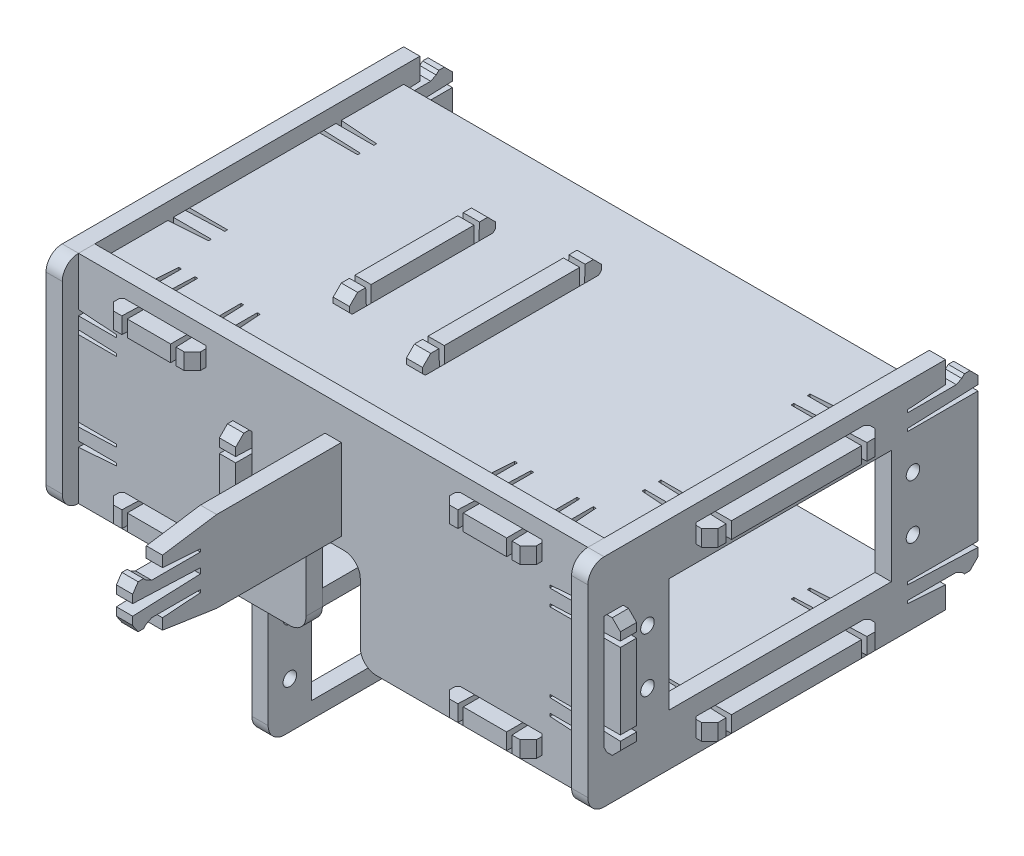
SolidWorks part; units mm, degrees
material "Lasercut ABS"
ref_plane "Front Plane" through (0, 0, 0) normal (0, 0, 1) x (1, 0, 0)
ref_plane "Top Plane" through (0, 0, 0) normal (0, 1, 0) x (1, 0, 0)
ref_plane "Right Plane" through (0, 0, 0) normal (1, 0, 0) x (0, 0, -1)
ref_plane "Plane1" through (47, 0, 0) normal (1, 0, 0) x (0, 0, -1)
ref_plane "Plane2" through (-47, 0, 0) normal (1, 0, 0) x (0, 0, -1)
sketch "Sketch1" plane through (47, 0, 0) normal (1, 0, 0) x (0, 0, -1)
  line L0 (36.5, 12) -> (36.5, -12)
  line L1 (-32.5, 10) -> (-29.5, 10)
  line L2 (-32.5, 10) -> (-32.5, -10)
  line L3 (-32.5, -10) -> (-29.5, -10)
  line L4 (-29.5, 10) -> (-29.5, -10)
  line L5 (-15, 17) -> (15, 17)
  line L6 (-15, 17) -> (-15, 14)
  line L7 (-15, 14) -> (15, 14)
  line L8 (15, 17) -> (15, 14)
  line L9 (-15, -14) -> (15, -14)
  line L10 (-15, -14) -> (-15, -17)
  line L11 (-15, -17) -> (15, -17)
  line L12 (15, -14) -> (15, -17)
  line L13 (30.5, 16) -> (30.5, 20)
  line L14 (30.5, 20) -> (-35.5, 20)
  line L15 (-35.5, 20) -> (-35.5, -20)
  line L16 (-35.5, -20) -> (30.5, -20)
  line L17 (30.5, -20) -> (30.5, -16)
  point P21 (0, -14)
  point P22 (-32.5, 0)
  point P23 (36.5, 0)
  line B0 (-24.5, 5) -> (-24.5, -5) construction
  line B1 (-20.5, -10.5) -> (20.5, -10.5)
  line B2 (-20.5, -10.5) -> (-20.5, 10.5)
  line B3 (-20.5, 10.5) -> (20.5, 10.5)
  line B4 (20.5, -10.5) -> (20.5, 10.5)
  line B5 (-20.5, -10.5) -> (20.5, 10.5) construction
  line B6 (-20.5, 10.5) -> (20.5, -10.5) construction
  line B7 (24.5, 5) -> (24.5, -5) construction
  line B8 (-24.5, 0) -> (24.5, 0) construction
  circle B9 centre (-24.5, 5) radius 1.25
  circle B10 centre (-24.5, -5) radius 1.25
  circle B11 centre (24.5, -5) radius 1.25
  circle B12 centre (24.5, 5) radius 1.25
  line B13 (23.5, -15.5) -> (30.5, -16)
  line B14 (23.5, -15) -> (23.5, -15.5)
  line B15 (32.5, -15) -> (23.5, -15)
  line B16 (33.5, -15.5) -> (32.5, -15)
  line B17 (34, -16) -> (33.5, -15.5)
  line B18 (35, -16) -> (34, -16)
  line B19 (36.5, -14.5) -> (35, -16)
  line B20 (36.5, -13) -> (36.5, -14.5)
  line B21 (23.5, -12) -> (23.5, -12.5)
  line B22 (23.5, -12.5) -> (36.5, -13)
  line B23 (36.5, -12) -> (23.5, -12)
  line B24 (36.5, 12) -> (23.5, 12)
  line B25 (23.5, 12) -> (23.5, 12.5)
  line B26 (23.5, 12.5) -> (36.5, 13)
  line B27 (36.5, 13) -> (36.5, 14.5)
  line B28 (36.5, 14.5) -> (35, 16)
  line B29 (35, 16) -> (34, 16)
  line B30 (34, 16) -> (33.5, 15.5)
  line B31 (33.5, 15.5) -> (32.5, 15)
  line B32 (32.5, 15) -> (23.5, 15)
  line B33 (23.5, 15) -> (23.5, 15.5)
  line B34 (23.5, 15.5) -> (30.5, 16)
  dimension "D1" = 3
  dimension "D2" = 14
  dimension "D3" = 14
  dimension "D4" = 3
  dimension "D5" = 3
  dimension "D6" = 30
  dimension "D7" = 30
  dimension "D8" = 9
  dimension "D9" = 3
  dimension "D10" = 20
  dimension "D11" = 3
sketch_block_instance "Block-Servo-Std-1"
sketch_block "Block-Servo-Std" parameters "D3"=2.5, "D1"=41, "D2"=21, "D4"=10, "D5"=49
sketch_block_instance "Block-Snap-L-1"
sketch_block "Block-Snap-L" parameters "D1"=13, "D2"=0.5, "D3"=1, "D4"=1.5, "D5"=1.5, "D6"=0.5, "D7"=1, "D8"=7, "D9"=1, "D10"=0.5, "D11"=1, "D12"=1.5, "D13"=2.5
sketch_block_instance "Block-Snap-R-1"
sketch_block "Block-Snap-R" parameters "D1"=13, "D2"=0.5, "D3"=1, "D4"=0.5, "D5"=1, "D6"=2.5, "D7"=1.5, "D8"=1.5, "D9"=1.5, "D10"=1, "D11"=0.5, "D12"=1, "D13"=7
extrude "Boss-Extrude1" add sketch "Sketch1" along normal blind 3 contours B33 B34 L13 L14 L15 L16 L17 B13 B14 B15 B16 B17 B18 B19 B20 B22 B21 B23 L0 B24 B25 B26 B27 B28 B29 B30 B31 B32 L9 L12 L11 L10 L1 L4 L3 L2 L5 L8 L7 L6 B4 B1 B2 B3 B9
mirror "Mirror2" about plane through (0, 0, 0) normal (1, 0, 0) of bodies 101
sketch "Sketch2" plane through (0, 0, 0) normal (1, 0, 0) x (0, 0, -1)
  line L0 (-13.5, 20) -> (11.5, 20)
  line L1 (15.5, 14) -> (27.5, 14)
  line L2 (27.5, 14) -> (27.5, -14)
  line L3 (27.5, -14) -> (24.5, -14)
  line L4 (-17.5, 14) -> (-55.5, 14)
  line L5 (-35.5, 20) -> (-35.5, -20) construction
  line L6 (-55.5, -1) -> (5.5, -1)
  line L7 (5.5, -1) -> (5.5, -14)
  line L8 (5.5, -14) -> (8.5, -14)
  line L9 (-15, 14) -> (15, 14) construction
  line L10 (30.5, 16) -> (30.5, 20) construction
  line L11 (-15, -14) -> (15, -14) construction
  line L12 (-29.5, 10) -> (-29.5, -10) construction
  line B0 (12.5, -20) -> (20.5, -20)
  line B1 (20.5, -20) -> (20.5, -7)
  line B2 (20.5, -7) -> (21, -7)
  line B3 (21, -7) -> (21.5, -20)
  line B4 (21.5, -20) -> (23, -20)
  line B5 (23, -20) -> (24.5, -18.5)
  line B6 (24.5, -18.5) -> (24.5, -17.5)
  line B7 (24.5, -17.5) -> (24, -17)
  line B8 (24, -17) -> (23.5, -16)
  line B9 (23.5, -16) -> (23.5, -7)
  line B10 (23.5, -7) -> (24, -7)
  line B11 (24, -7) -> (24.5, -14)
  line B12 (16.5, -20) -> (16.5, -7) construction
  line B13 (9, -7) -> (8.5, -14)
  line B14 (9.5, -7) -> (9, -7)
  line B15 (9.5, -16) -> (9.5, -7)
  line B16 (9, -17) -> (9.5, -16)
  line B17 (8.5, -17.5) -> (9, -17)
  line B18 (8.5, -18.5) -> (8.5, -17.5)
  line B19 (10, -20) -> (8.5, -18.5)
  line B20 (11.5, -20) -> (10, -20)
  line B21 (12.5, -7) -> (12, -7)
  line B22 (12, -7) -> (11.5, -20)
  line B23 (12.5, -20) -> (12.5, -7)
  line B24 (15, 7) -> (15.5, 14)
  line B25 (14.5, 7) -> (15, 7)
  line B26 (14.5, 16) -> (14.5, 7)
  line B27 (15, 17) -> (14.5, 16)
  line B28 (15.5, 17.5) -> (15, 17)
  line B29 (15.5, 18.5) -> (15.5, 17.5)
  line B30 (14, 20) -> (15.5, 18.5)
  line B31 (12.5, 20) -> (14, 20)
  line B32 (11.5, 7) -> (12, 7)
  line B33 (12, 7) -> (12.5, 20)
  line B34 (11.5, 20) -> (11.5, 7)
  line B35 (-13.5, 20) -> (-13.5, 7)
  line B36 (-13.5, 7) -> (-14, 7)
  line B37 (-14, 7) -> (-14.5, 20)
  line B38 (-14.5, 20) -> (-16, 20)
  line B39 (-16, 20) -> (-17.5, 18.5)
  line B40 (-17.5, 18.5) -> (-17.5, 17.5)
  line B41 (-17.5, 17.5) -> (-17, 17)
  line B42 (-17, 17) -> (-16.5, 16)
  line B43 (-16.5, 16) -> (-16.5, 7)
  line B44 (-16.5, 7) -> (-17, 7)
  line B45 (-17, 7) -> (-17.5, 14)
  line B46 (-55.5, 6.5) -> (-58.5, 6.5) construction
  line B47 (-58.5, 6) -> (-58.5, 7)
  line B48 (-58.5, 6) -> (-71, 5.5)
  line B49 (-71, 5.5) -> (-71, 4)
  line B50 (-71, 4) -> (-70, 2.5)
  line B51 (-70, 2.5) -> (-69, 2.5)
  line B52 (-69, 2.5) -> (-68.5, 3)
  line B53 (-68.5, 3) -> (-67.5, 3.5)
  line B54 (-67.5, 3.5) -> (-58.5, 3.5)
  line B55 (-58.5, 3.5) -> (-58.5, 3)
  line B56 (-58.5, 3) -> (-65.5, 2.5)
  line B57 (-65.5, 2.5) -> (-65.5, 0.5)
  line B58 (-65.5, 0.5) -> (-55.5, -1)
  line B59 (-58.5, 7) -> (-71, 7.5)
  line B60 (-71, 7.5) -> (-71, 9)
  line B61 (-71, 9) -> (-70, 10.5)
  line B62 (-70, 10.5) -> (-69, 10.5)
  line B63 (-69, 10.5) -> (-68.5, 10)
  line B64 (-68.5, 10) -> (-67.5, 9.5)
  line B65 (-67.5, 9.5) -> (-58.5, 9.5)
  line B66 (-58.5, 9.5) -> (-58.5, 10)
  line B67 (-58.5, 10) -> (-65.5, 10.5)
  line B68 (-65.5, 10.5) -> (-65.5, 12.5)
  line B69 (-65.5, 12.5) -> (-55.5, 14)
  dimension "D1" = 3
  dimension "D2" = 22
  dimension "D3" = 30
  dimension "D4" = 12
  dimension "D6" = 12
sketch_block_instance "Block-Snap-14mm-1"
sketch_block "Block-Snap-14mm" parameters "D1"=8, "D2"=13, "D3"=0.5, "D4"=1, "D5"=0.5, "D6"=1, "D7"=2.5, "D8"=1.5, "D9"=1.5, "D10"=1.5, "D11"=1, "D12"=0.5, "D13"=1, "D14"=7
sketch_block_instance "Block-Snap-L-3"
sketch_block_instance "Block-Snap-R-3"
sketch_block_instance "Block-Snap-Textile-1"
sketch_block "Block-Snap-Textile" parameters "D1"=3, "D2"=1, "D3"=2, "D4"=1.5, "D5"=10, "D6"=0.5, "D7"=9, "D8"=1, "D9"=0.5, "D10"=0.5, "D11"=0.5, "D12"=1, "D13"=12.5, "D14"=0.5, "D15"=0.5, "D16"=1.5, "D17"=1.5
extrude "Boss-Extrude2" add sketch "Sketch2" along normal mid plane 3 separate body
ref_plane "Plane3" through (-16.5, 0, 0) normal (1, 0, 0) x (0, 0, -1)
sketch "Sketch3" plane through (0, 14, 0) normal (0, 1, 0) x (1, 0, 0)
  line L0 (-53, 12) -> (-53, -12)
  line L1 (-1.5, -16.5) -> (1.5, -16.5)
  line L2 (-1.5, -16.5) -> (-1.5, 14.5)
  line L3 (-1.5, 14.5) -> (1.5, 14.5)
  line L4 (1.5, -16.5) -> (1.5, 14.5)
  line L5 (53, 12) -> (53, -12)
  line L6 (-47, 16) -> (-47, 27.5)
  line L7 (-47, 27.5) -> (47, 27.5)
  line L8 (47, 27.5) -> (47, 16)
  line L9 (47, 30.5) -> (47, -35.5) construction
  line L10 (-47, 30.5) -> (-47, -35.5) construction
  line L11 (50, 15) -> (47, 15) construction
  line L12 (50, -15) -> (47, -15) construction
  line L13 (-50, -15) -> (-47, -15) construction
  line L14 (-50, 15) -> (-47, 15) construction
  line L15 (1.5, 27.5) -> (-1.5, 27.5) construction
  line L16 (47, -16) -> (47, -29.5)
  line L17 (47, -29.5) -> (39, -29.5)
  line L18 (23, -29.5) -> (-23, -29.5)
  line L19 (-39, -29.5) -> (-47, -29.5)
  line L20 (-47, -29.5) -> (-47, -16)
  line L21 (-16.5, -22) -> (-16.5, 22) construction
  line L22 (-18, -13.5) -> (-15, -13.5)
  line L23 (-18, -13.5) -> (-18, 11.5)
  line L24 (-18, 11.5) -> (-15, 11.5)
  line L25 (-15, -13.5) -> (-15, 11.5)
  point P41 (-16.5, -13.5)
  line B0 (40, -15.5) -> (47, -16)
  line B1 (40, -15) -> (40, -15.5)
  line B2 (49, -15) -> (40, -15)
  line B3 (50, -15.5) -> (49, -15)
  line B4 (50.5, -16) -> (50, -15.5)
  line B5 (51.5, -16) -> (50.5, -16)
  line B6 (53, -14.5) -> (51.5, -16)
  line B7 (53, -13) -> (53, -14.5)
  line B8 (40, -12) -> (40, -12.5)
  line B9 (40, -12.5) -> (53, -13)
  line B10 (53, -12) -> (40, -12)
  line B11 (-40, 15.5) -> (-47, 16)
  line B12 (-40, 15) -> (-40, 15.5)
  line B13 (-49, 15) -> (-40, 15)
  line B14 (-50, 15.5) -> (-49, 15)
  line B15 (-50.5, 16) -> (-50, 15.5)
  line B16 (-51.5, 16) -> (-50.5, 16)
  line B17 (-53, 14.5) -> (-51.5, 16)
  line B18 (-53, 13) -> (-53, 14.5)
  line B19 (-40, 12) -> (-40, 12.5)
  line B20 (-40, 12.5) -> (-53, 13)
  line B21 (-53, 12) -> (-40, 12)
  line B22 (-53, -12) -> (-40, -12)
  line B23 (-40, -12) -> (-40, -12.5)
  line B24 (-40, -12.5) -> (-53, -13)
  line B25 (-53, -13) -> (-53, -14.5)
  line B26 (-53, -14.5) -> (-51.5, -16)
  line B27 (-51.5, -16) -> (-50.5, -16)
  line B28 (-50.5, -16) -> (-50, -15.5)
  line B29 (-50, -15.5) -> (-49, -15)
  line B30 (-49, -15) -> (-40, -15)
  line B31 (-40, -15) -> (-40, -15.5)
  line B32 (-40, -15.5) -> (-47, -16)
  line B33 (53, 12) -> (40, 12)
  line B34 (40, 12) -> (40, 12.5)
  line B35 (40, 12.5) -> (53, 13)
  line B36 (53, 13) -> (53, 14.5)
  line B37 (53, 14.5) -> (51.5, 16)
  line B38 (51.5, 16) -> (50.5, 16)
  line B39 (50.5, 16) -> (50, 15.5)
  line B40 (50, 15.5) -> (49, 15)
  line B41 (49, 15) -> (40, 15)
  line B42 (40, 15) -> (40, 15.5)
  line B43 (40, 15.5) -> (47, 16)
  line B44 (27, -35.5) -> (35, -35.5)
  line B45 (35, -35.5) -> (35, -22.5)
  line B46 (35, -22.5) -> (35.5, -22.5)
  line B47 (35.5, -22.5) -> (36, -35.5)
  line B48 (36, -35.5) -> (37.5, -35.5)
  line B49 (37.5, -35.5) -> (39, -34)
  line B50 (39, -34) -> (39, -33)
  line B51 (39, -33) -> (38.5, -32.5)
  line B52 (38.5, -32.5) -> (38, -31.5)
  line B53 (38, -31.5) -> (38, -22.5)
  line B54 (38, -22.5) -> (38.5, -22.5)
  line B55 (38.5, -22.5) -> (39, -29.5)
  line B56 (31, -35.5) -> (31, -22.5) construction
  line B57 (23.5, -22.5) -> (23, -29.5)
  line B58 (24, -22.5) -> (23.5, -22.5)
  line B59 (24, -31.5) -> (24, -22.5)
  line B60 (23.5, -32.5) -> (24, -31.5)
  line B61 (23, -33) -> (23.5, -32.5)
  line B62 (23, -34) -> (23, -33)
  line B63 (24.5, -35.5) -> (23, -34)
  line B64 (26, -35.5) -> (24.5, -35.5)
  line B65 (27, -22.5) -> (26.5, -22.5)
  line B66 (26.5, -22.5) -> (26, -35.5)
  line B67 (27, -35.5) -> (27, -22.5)
  line B68 (-35, -35.5) -> (-27, -35.5)
  line B69 (-27, -35.5) -> (-27, -22.5)
  line B70 (-27, -22.5) -> (-26.5, -22.5)
  line B71 (-26.5, -22.5) -> (-26, -35.5)
  line B72 (-26, -35.5) -> (-24.5, -35.5)
  line B73 (-24.5, -35.5) -> (-23, -34)
  line B74 (-23, -34) -> (-23, -33)
  line B75 (-23, -33) -> (-23.5, -32.5)
  line B76 (-23.5, -32.5) -> (-24, -31.5)
  line B77 (-24, -31.5) -> (-24, -22.5)
  line B78 (-24, -22.5) -> (-23.5, -22.5)
  line B79 (-23.5, -22.5) -> (-23, -29.5)
  line B80 (-31, -35.5) -> (-31, -22.5) construction
  line B81 (-38.5, -22.5) -> (-39, -29.5)
  line B82 (-38, -22.5) -> (-38.5, -22.5)
  line B83 (-38, -31.5) -> (-38, -22.5)
  line B84 (-38.5, -32.5) -> (-38, -31.5)
  line B85 (-39, -33) -> (-38.5, -32.5)
  line B86 (-39, -34) -> (-39, -33)
  line B87 (-37.5, -35.5) -> (-39, -34)
  line B88 (-36, -35.5) -> (-37.5, -35.5)
  line B89 (-35, -22.5) -> (-35.5, -22.5)
  line B90 (-35.5, -22.5) -> (-36, -35.5)
  line B91 (-35, -35.5) -> (-35, -22.5)
  line M1 (47, 15) -> (47, -15)
  line M2 (47, -15) -> (50, -15)
  line M3 (50, -15) -> (50, 15)
  line M4 (50, 15) -> (47, 15)
  dimension "D1" = 8
  dimension "D2" = 3
  dimension "D3" = 16
  dimension "D4" = 16
sketch_block_instance "Block-Snap-L-5"
sketch_block_instance "Block-Snap-L-6"
sketch_block_instance "Block-Snap-R-5"
sketch_block_instance "Block-Snap-R-6"
sketch_block_instance "Block-Snap-14mm-3"
sketch_block_instance "Block-Snap-14mm-4"
extrude "Boss-Extrude3" add sketch "Sketch3" along normal blind 3 separate body contours B91 B68 B69 B70 B71 B72 B73 B74 B75 B76 B77 B78 B79 L18 B57 B58 B59 B60 B61 B62 B63 B64 B66 B65 B67 B44 B45 B46 B47 B48 B49 B50 B51 B52 B53 B54 B55 L17 L16 B0 B1 B2 B9 B8 B10 B33 B34 B35 M1 | B35 M1 M3 M4 | B33 B10 M3 M1 | L5 B33 B10 M3 | B39 B40 B35 B36 B37 B38 M4 M3 | B9 M1 M2 M3 | B9 B3 B4 B5 B6 B7 M3 M2
ref_plane "Plane4" through (0, -17, 0) normal (0, 1, 0) x (1, 0, 0)
sketch "Sketch4" plane through (0, -17, 0) normal (0, 1, 0) x (1, 0, 0)
  line L0 (-53, -12) -> (-53, 12)
  line L1 (1.5, 9.5) -> (-1.5, 9.5)
  line L2 (1.5, 9.5) -> (1.5, 23.5)
  line L3 (1.5, 23.5) -> (-1.5, 23.5)
  line L4 (-1.5, 9.5) -> (-1.5, 23.5)
  line L5 (53, -12) -> (53, 12)
  line L6 (47, 16) -> (47, 27.5)
  line L7 (47, 27.5) -> (-47, 27.5)
  line L8 (-47, 27.5) -> (-47, 16)
  line L9 (50, 15) -> (47, 15) construction
  line L10 (50, -15) -> (47, -15) construction
  line L11 (-50, 15) -> (-47, 15) construction
  line L12 (-50, -15) -> (-47, -15) construction
  line L13 (-47, -16) -> (-47, -29.5)
  line L14 (-47, -29.5) -> (-39, -29.5)
  line L15 (47, -16) -> (47, -29.5)
  line L16 (47, -29.5) -> (39, -29.5)
  line L18 (-23, -29.5) -> (-18, -29.5)
  line L19 (-18, -29.5) -> (-18, 7.5)
  line L20 (-18, 7.5) -> (-15, 7.5)
  line L21 (-15, 7.5) -> (-15, -29.5)
  line L22 (-18, -13.5) -> (-18, 11.5) construction
  line L23 (-15, -13.5) -> (-15, 11.5) construction
  line L24 (-15, -29.5) -> (-5, -29.5)
  line L25 (-5, -29.5) -> (-5, 5.5)
  line L26 (-5, 5.5) -> (5, 5.5)
  line L27 (5, 5.5) -> (5, -29.5)
  line L28 (5, -29.5) -> (23, -29.5)
  line L29 (0, 0) -> (0, 5.5) construction
  line L30 (1.5, 5.5) -> (-1.5, 5.5) construction
  line B0 (40, -15.5) -> (47, -16)
  line B1 (40, -15) -> (40, -15.5)
  line B2 (49, -15) -> (40, -15)
  line B3 (50, -15.5) -> (49, -15)
  line B4 (50.5, -16) -> (50, -15.5)
  line B5 (51.5, -16) -> (50.5, -16)
  line B6 (53, -14.5) -> (51.5, -16)
  line B7 (53, -13) -> (53, -14.5)
  line B8 (40, -12) -> (40, -12.5)
  line B9 (40, -12.5) -> (53, -13)
  line B10 (53, -12) -> (40, -12)
  line B11 (-40, 15.5) -> (-47, 16)
  line B12 (-40, 15) -> (-40, 15.5)
  line B13 (-49, 15) -> (-40, 15)
  line B14 (-50, 15.5) -> (-49, 15)
  line B15 (-50.5, 16) -> (-50, 15.5)
  line B16 (-51.5, 16) -> (-50.5, 16)
  line B17 (-53, 14.5) -> (-51.5, 16)
  line B18 (-53, 13) -> (-53, 14.5)
  line B19 (-40, 12) -> (-40, 12.5)
  line B20 (-40, 12.5) -> (-53, 13)
  line B21 (-53, 12) -> (-40, 12)
  line B22 (53, 12) -> (40, 12)
  line B23 (40, 12) -> (40, 12.5)
  line B24 (40, 12.5) -> (53, 13)
  line B25 (53, 13) -> (53, 14.5)
  line B26 (53, 14.5) -> (51.5, 16)
  line B27 (51.5, 16) -> (50.5, 16)
  line B28 (50.5, 16) -> (50, 15.5)
  line B29 (50, 15.5) -> (49, 15)
  line B30 (49, 15) -> (40, 15)
  line B31 (40, 15) -> (40, 15.5)
  line B32 (40, 15.5) -> (47, 16)
  line B33 (-53, -12) -> (-40, -12)
  line B34 (-40, -12) -> (-40, -12.5)
  line B35 (-40, -12.5) -> (-53, -13)
  line B36 (-53, -13) -> (-53, -14.5)
  line B37 (-53, -14.5) -> (-51.5, -16)
  line B38 (-51.5, -16) -> (-50.5, -16)
  line B39 (-50.5, -16) -> (-50, -15.5)
  line B40 (-50, -15.5) -> (-49, -15)
  line B41 (-49, -15) -> (-40, -15)
  line B42 (-40, -15) -> (-40, -15.5)
  line B43 (-40, -15.5) -> (-47, -16)
  line B44 (27, -35.5) -> (35, -35.5)
  line B45 (35, -35.5) -> (35, -22.5)
  line B46 (35, -22.5) -> (35.5, -22.5)
  line B47 (35.5, -22.5) -> (36, -35.5)
  line B48 (36, -35.5) -> (37.5, -35.5)
  line B49 (37.5, -35.5) -> (39, -34)
  line B50 (39, -34) -> (39, -33)
  line B51 (39, -33) -> (38.5, -32.5)
  line B52 (38.5, -32.5) -> (38, -31.5)
  line B53 (38, -31.5) -> (38, -22.5)
  line B54 (38, -22.5) -> (38.5, -22.5)
  line B55 (38.5, -22.5) -> (39, -29.5)
  line B56 (31, -35.5) -> (31, -22.5) construction
  line B57 (23.5, -22.5) -> (23, -29.5)
  line B58 (24, -22.5) -> (23.5, -22.5)
  line B59 (24, -31.5) -> (24, -22.5)
  line B60 (23.5, -32.5) -> (24, -31.5)
  line B61 (23, -33) -> (23.5, -32.5)
  line B62 (23, -34) -> (23, -33)
  line B63 (24.5, -35.5) -> (23, -34)
  line B64 (26, -35.5) -> (24.5, -35.5)
  line B65 (27, -22.5) -> (26.5, -22.5)
  line B66 (26.5, -22.5) -> (26, -35.5)
  line B67 (27, -35.5) -> (27, -22.5)
  line B68 (-35, -35.5) -> (-27, -35.5)
  line B69 (-27, -35.5) -> (-27, -22.5)
  line B70 (-27, -22.5) -> (-26.5, -22.5)
  line B71 (-26.5, -22.5) -> (-26, -35.5)
  line B72 (-26, -35.5) -> (-24.5, -35.5)
  line B73 (-24.5, -35.5) -> (-23, -34)
  line B74 (-23, -34) -> (-23, -33)
  line B75 (-23, -33) -> (-23.5, -32.5)
  line B76 (-23.5, -32.5) -> (-24, -31.5)
  line B77 (-24, -31.5) -> (-24, -22.5)
  line B78 (-24, -22.5) -> (-23.5, -22.5)
  line B79 (-23.5, -22.5) -> (-23, -29.5)
  line B80 (-31, -35.5) -> (-31, -22.5) construction
  line B81 (-38.5, -22.5) -> (-39, -29.5)
  line B82 (-38, -22.5) -> (-38.5, -22.5)
  line B83 (-38, -31.5) -> (-38, -22.5)
  line B84 (-38.5, -32.5) -> (-38, -31.5)
  line B85 (-39, -33) -> (-38.5, -32.5)
  line B86 (-39, -34) -> (-39, -33)
  line B87 (-37.5, -35.5) -> (-39, -34)
  line B88 (-36, -35.5) -> (-37.5, -35.5)
  line B89 (-35, -22.5) -> (-35.5, -22.5)
  line B90 (-35.5, -22.5) -> (-36, -35.5)
  line B91 (-35, -35.5) -> (-35, -22.5)
  dimension "D1" = 20
  dimension "D2" = 10
sketch_block_instance "Block-Snap-L-8"
sketch_block_instance "Block-Snap-L-9"
sketch_block_instance "Block-Snap-R-8"
sketch_block_instance "Block-Snap-R-9"
sketch_block_instance "Block-Snap-14mm-6"
sketch_block_instance "Block-Snap-14mm-7"
extrude "Boss-Extrude4" add sketch "Sketch4" along normal blind 3 separate body contours B91 B68 B69 B70 B71 B72 B73 B74 B75 B76 B77 B78 B79 L18 L19 L20 L21 L24 L25 L26 L27 L28 B57 B58 B59 B60 B61 B62 B63 B64 B66 B65 B67 B44 B45 B46 B47 B48 B49 B50 B51 B52 B53 B54 B55 L16 L15 B0 B1 B2
ref_plane "Plane5" through (-18, 0, 0) normal (1, 0, 0) x (0, 0, -1)
sketch "Sketch5" plane through (-18, 0, 0) normal (1, 0, 0) x (0, 0, -1)
  line L0 (7.5, -14) -> (27.5, -14)
  line L1 (7.5, -14) -> (7.5, -17)
  line L2 (7.5, -17) -> (27.5, -17)
  line L3 (27.5, -14) -> (27.5, 14)
  line L4 (27.5, 14) -> (12.5, 14)
  line L5 (27.5, -17) -> (27.5, -44)
  line L6 (27.5, -44) -> (-29.5, -44)
  line L7 (8.5, 20) -> (-10.5, 20)
  line L8 (11.5, 17) -> (11.5, 14) construction
  line L9 (-13.5, 17) -> (-13.5, 14) construction
  line L10 (-14.5, 14) -> (-29.5, 14)
  line L11 (-29.5, -8) -> (-29.5, -44)
  line L12 (-29.5, 14) -> (-29.5, 8)
  line L14 (-1, -30.5) -> (-1, -44) construction
  point P27 (0, 0)
  line B0 (12, 7) -> (12.5, 14)
  line B1 (11.5, 7) -> (12, 7)
  line B2 (11.5, 16) -> (11.5, 7)
  line B3 (12, 17) -> (11.5, 16)
  line B4 (12.5, 17.5) -> (12, 17)
  line B5 (12.5, 18.5) -> (12.5, 17.5)
  line B6 (11, 20) -> (12.5, 18.5)
  line B7 (9.5, 20) -> (11, 20)
  line B8 (8.5, 7) -> (9, 7)
  line B9 (9, 7) -> (9.5, 20)
  line B10 (8.5, 20) -> (8.5, 7)
  line B11 (-10.5, 20) -> (-10.5, 7)
  line B12 (-10.5, 7) -> (-11, 7)
  line B13 (-11, 7) -> (-11.5, 20)
  line B14 (-11.5, 20) -> (-13, 20)
  line B15 (-13, 20) -> (-14.5, 18.5)
  line B16 (-14.5, 18.5) -> (-14.5, 17.5)
  line B17 (-14.5, 17.5) -> (-14, 17)
  line B18 (-14, 17) -> (-13.5, 16)
  line B19 (-13.5, 16) -> (-13.5, 7)
  line B20 (-13.5, 7) -> (-14, 7)
  line B21 (-14, 7) -> (-14.5, 14)
  line B22 (-35.5, 4) -> (-35.5, -4)
  line B23 (-35.5, -4) -> (-22.5, -4)
  line B24 (-22.5, -4) -> (-22.5, -4.5)
  line B25 (-22.5, -4.5) -> (-35.5, -5)
  line B26 (-35.5, -5) -> (-35.5, -6.5)
  line B27 (-35.5, -6.5) -> (-34, -8)
  line B28 (-34, -8) -> (-33, -8)
  line B29 (-33, -8) -> (-32.5, -7.5)
  line B30 (-32.5, -7.5) -> (-31.5, -7)
  line B31 (-31.5, -7) -> (-22.5, -7)
  line B32 (-22.5, -7) -> (-22.5, -7.5)
  line B33 (-22.5, -7.5) -> (-29.5, -8)
  line B34 (-35.5, 0) -> (-22.5, 0) construction
  line B35 (-22.5, 7.5) -> (-29.5, 8)
  line B36 (-22.5, 7) -> (-22.5, 7.5)
  line B37 (-31.5, 7) -> (-22.5, 7)
  line B38 (-32.5, 7.5) -> (-31.5, 7)
  line B39 (-33, 8) -> (-32.5, 7.5)
  line B40 (-34, 8) -> (-33, 8)
  line B41 (-35.5, 6.5) -> (-34, 8)
  line B42 (-35.5, 5) -> (-35.5, 6.5)
  line B43 (-22.5, 4) -> (-22.5, 4.5)
  line B44 (-22.5, 4.5) -> (-35.5, 5)
  line B45 (-35.5, 4) -> (-22.5, 4)
  line B46 (-25.5, -25.5) -> (-25.5, -35.5) construction
  line B47 (-21.5, -41) -> (19.5, -41)
  line B48 (-21.5, -41) -> (-21.5, -20)
  line B49 (-21.5, -20) -> (19.5, -20)
  line B50 (19.5, -41) -> (19.5, -20)
  line B51 (-21.5, -41) -> (19.5, -20) construction
  line B52 (-21.5, -20) -> (19.5, -41) construction
  line B53 (23.5, -25.5) -> (23.5, -35.5) construction
  line B54 (-25.5, -30.5) -> (23.5, -30.5) construction
  circle B55 centre (-25.5, -25.5) radius 1.25
  circle B56 centre (-25.5, -35.5) radius 1.25
  circle B57 centre (23.5, -35.5) radius 1.25
  circle B58 centre (23.5, -25.5) radius 1.25
  dimension "D1" = 3
  dimension "D2" = 3
sketch_block_instance "Block-Snap-L-11"
sketch_block_instance "Block-Snap-R-11"
sketch_block_instance "Block-Snap-14mm-9"
sketch_block_instance "Block-Servo-Std-13"
extrude "Boss-Extrude5" add sketch "Sketch5" along normal blind 3 separate body
ref_plane "Plane6" through (0, 0, 29.5) normal (0, 0, 1) x (1, 0, 0)
sketch "Sketch6" plane through (0, 0, 29.5) normal (0, 0, 1) x (1, 0, 0)
  line L0 (-53, -7) -> (-53, 7)
  line L1 (-38, -14) -> (-24, -14)
  line L2 (-38, -14) -> (-38, -17)
  line L3 (-38, -17) -> (-24, -17)
  line L4 (-24, -14) -> (-24, -17)
  line L5 (24, -14) -> (38, -14)
  line L6 (24, -14) -> (24, -17)
  line L7 (24, -17) -> (38, -17)
  line L8 (38, -14) -> (38, -17)
  line L9 (-38, 17) -> (-24, 17)
  line L10 (-38, 17) -> (-38, 14)
  line L11 (-38, 14) -> (-24, 14)
  line L12 (-24, 17) -> (-24, 14)
  line L13 (24, 17) -> (38, 17)
  line L14 (24, 17) -> (24, 14)
  line L15 (24, 14) -> (38, 14)
  line L16 (38, 17) -> (38, 14)
  line L17 (-18, 7) -> (-15, 7)
  line L18 (-18, 7) -> (-18, -7)
  line L19 (-18, -7) -> (-15, -7)
  line L20 (-15, 7) -> (-15, -7)
  line L21 (-1.5, 14) -> (1.5, 14)
  line L22 (-1.5, 14) -> (-1.5, -1)
  line L23 (-1.5, -1) -> (1.5, -1)
  line L24 (1.5, 14) -> (1.5, -1)
  line L25 (53, 7) -> (53, -7)
  line L26 (-47, 11) -> (-47, 20)
  line L27 (-47, 20) -> (47, 20)
  line L28 (47, 20) -> (47, 11)
  line L30 (-47, -11) -> (-47, -20)
  line L31 (-47, -20) -> (-5, -20)
  line L32 (47, -20) -> (47, -11)
  line L33 (-50, 10) -> (-47, 10) construction
  line L34 (-50, -10) -> (-47, -10) construction
  line L35 (50, 10) -> (47, 10) construction
  line L36 (50, -10) -> (47, -10) construction
  line L37 (5, -20) -> (47, -20)
  line L38 (-5, -14) -> (-5, -17) construction
  line L39 (-5, -20) -> (-5, -3)
  line L40 (-5, -3) -> (5, -3)
  line L41 (5, -20) -> (5, -3)
  line L42 (5, -14) -> (5, -17) construction
  line B0 (-40, 10.5) -> (-47, 11)
  line B1 (-40, 10) -> (-40, 10.5)
  line B2 (-49, 10) -> (-40, 10)
  line B3 (-50, 10.5) -> (-49, 10)
  line B4 (-50.5, 11) -> (-50, 10.5)
  line B5 (-51.5, 11) -> (-50.5, 11)
  line B6 (-53, 9.5) -> (-51.5, 11)
  line B7 (-53, 8) -> (-53, 9.5)
  line B8 (-40, 7) -> (-40, 7.5)
  line B9 (-40, 7.5) -> (-53, 8)
  line B10 (-53, 7) -> (-40, 7)
  line B11 (40, -10.5) -> (47, -11)
  line B12 (40, -10) -> (40, -10.5)
  line B13 (49, -10) -> (40, -10)
  line B14 (50, -10.5) -> (49, -10)
  line B15 (50.5, -11) -> (50, -10.5)
  line B16 (51.5, -11) -> (50.5, -11)
  line B17 (53, -9.5) -> (51.5, -11)
  line B18 (53, -8) -> (53, -9.5)
  line B19 (40, -7) -> (40, -7.5)
  line B20 (40, -7.5) -> (53, -8)
  line B21 (53, -7) -> (40, -7)
  line B22 (-53, -7) -> (-40, -7)
  line B23 (-40, -7) -> (-40, -7.5)
  line B24 (-40, -7.5) -> (-53, -8)
  line B25 (-53, -8) -> (-53, -9.5)
  line B26 (-53, -9.5) -> (-51.5, -11)
  line B27 (-51.5, -11) -> (-50.5, -11)
  line B28 (-50.5, -11) -> (-50, -10.5)
  line B29 (-50, -10.5) -> (-49, -10)
  line B30 (-49, -10) -> (-40, -10)
  line B31 (-40, -10) -> (-40, -10.5)
  line B32 (-40, -10.5) -> (-47, -11)
  line B33 (53, 7) -> (40, 7)
  line B34 (40, 7) -> (40, 7.5)
  line B35 (40, 7.5) -> (53, 8)
  line B36 (53, 8) -> (53, 9.5)
  line B37 (53, 9.5) -> (51.5, 11)
  line B38 (51.5, 11) -> (50.5, 11)
  line B39 (50.5, 11) -> (50, 10.5)
  line B40 (50, 10.5) -> (49, 10)
  line B41 (49, 10) -> (40, 10)
  line B42 (40, 10) -> (40, 10.5)
  line B43 (40, 10.5) -> (47, 11)
  dimension "D1" = 2
sketch_block_instance "Block-Snap-L-13"
sketch_block_instance "Block-Snap-L-14"
sketch_block_instance "Block-Snap-R-13"
sketch_block_instance "Block-Snap-R-14"
extrude "Boss-Extrude6" add sketch "Sketch6" along normal blind 3 separate body contours B42 B43 L28 L27 L26 B0 B1 B2 B3 B4 B5 B6 B7 B9 B8 B10 L0 B22 B23 B24 B25 B26 B27 B28 B29 B30 B31 B32 L30 L31 L39 L40 L41 L37 L32 B11 B12 B13 B14 B15 B16 B17 B18 B20 B19 B21 L25 B33 B34 B35 B36
fillet "Fillet1" radius 3 2 edges at (-16.5, -44, -27.5) (-16.5, -44, 29.5)
fillet "Fillet2" radius 3 4 edges at (5, -20, 31) (-5, -20, 31) (5, -3, 31) (-5, -3, 31)
fillet "Fillet3" radius 3 2 edges at (-48.5, -20, 35.5) (-48.5, 20, 35.5)
fillet "Fillet4" radius 3 2 edges at (48.5, 20, 35.5) (48.5, -20, 35.5)
fillet "Fillet5" radius 3 2 edges at (5, -15.5, -5.5) (-5, -15.5, -5.5)
other "Save Bodies1"
